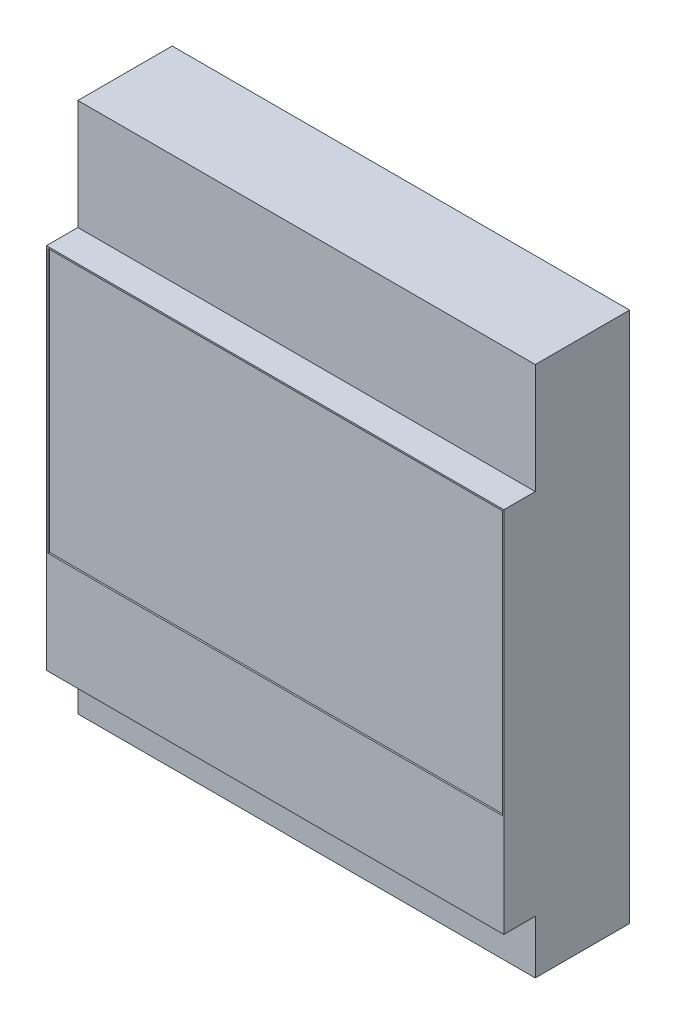
SolidWorks part; units mm, degrees
ref_plane "Спереди" through (0, 0, 0) normal (0, 0, 1) x (1, 0, 0)
ref_plane "Сверху" through (0, 0, 0) normal (0, 1, 0) x (1, 0, 0)
ref_plane "Справа" through (0, 0, 0) normal (1, 0, 0) x (0, 0, -1)
sketch "Эскиз1" plane through (0, 0, 0) normal (0, 0, 1) x (1, 0, 0)
  line L1 (-7.275, -5.85) -> (7.275, -5.85)
  line L2 (-7.275, -5.85) -> (-7.275, 5.85)
  line L3 (-7.275, 5.85) -> (7.275, 5.85)
  line L4 (7.275, -5.85) -> (7.275, 5.85)
  line L5 (-7.275, -5.85) -> (7.275, 5.85) construction
  line L6 (-7.275, 5.85) -> (7.275, -5.85) construction
  point P0 (0, 0)
  dimension "D1" = 14.55
  dimension "D2" = 11.7
extrude "Бобышка-Вытянуть1" add sketch "Эскиз1" along normal blind 1
sketch "Эскиз2" plane through (0, 0, 1) normal (0, 0, 1) x (1, 0, 0)
  line L0 (7.275, 5.85) -> (-7.275, 5.85) construction
  line L1 (-7.225, 5.8) -> (7.225, 5.8)
  line L2 (-7.225, 5.8) -> (-7.225, -2.6)
  line L3 (-7.225, -2.6) -> (7.225, -2.6)
  line L4 (7.225, 5.8) -> (7.225, -2.6)
  line L5 (7.275, -5.85) -> (7.275, 5.85) construction
  line L6 (-7.275, 5.85) -> (-7.275, -5.85) construction
  dimension "D1" = 0.05
  dimension "D2" = 0.05
  dimension "D3" = 0.05
  dimension "D4" = 8.45
extrude "Вырез-Вытянуть1" cut sketch "Эскиз2" against normal blind 0.05
sketch "Эскиз3" plane through (0, 0, 0) normal (0, 0, -1) x (-1, 0, 0)
  line L0 (7.275, 5.85) -> (7.275, -5.85) construction
  line L1 (-7.275, 9.35) -> (7.275, 9.35)
  line L2 (-7.275, 9.35) -> (-7.275, -7.55)
  line L3 (-7.275, -7.55) -> (7.275, -7.55)
  line L4 (7.275, 9.35) -> (7.275, -7.55)
  line L5 (-7.275, -5.85) -> (-7.275, 5.85) construction
  line L6 (7.275, -5.85) -> (-7.275, -5.85) construction
  line L7 (-7.275, 5.85) -> (7.275, 5.85) construction
  dimension "D1" = 1.7
  dimension "D2" = 3.5
extrude "Бобышка-Вытянуть2" add sketch "Эскиз3" along normal blind 3
